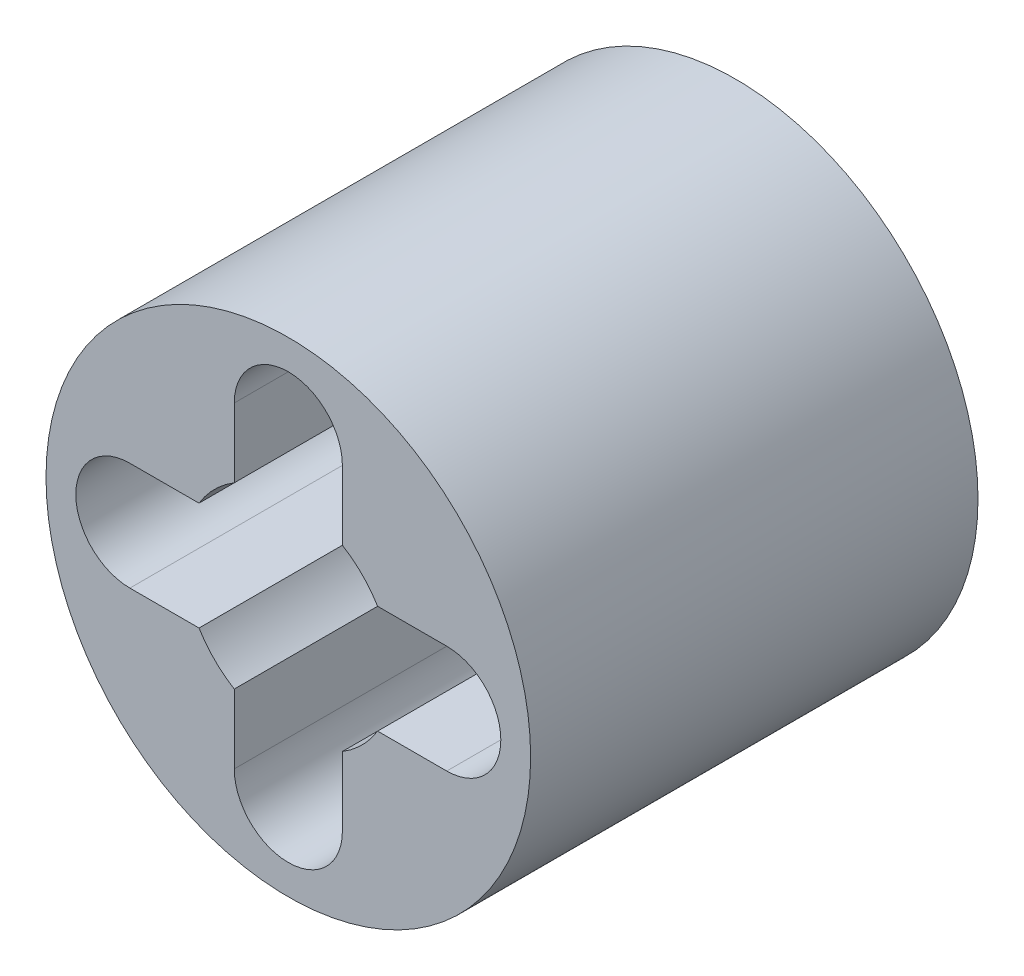
SolidWorks part; units mm, degrees
ref_plane "Plan de face" through (0, 0, 0) normal (0, 0, 1) x (1, 0, 0)
ref_plane "Plan de dessus" through (0, 0, 0) normal (0, 1, 0) x (1, 0, 0)
ref_plane "Plan de droite" through (0, 0, 0) normal (1, 0, 0) x (0, 0, -1)
sketch "Esquisse1" plane through (0, 0, 0) normal (0, 0, 1) x (1, 0, 0)
  line L0 (2.125, -0.725) -> (1.1977, -0.725)
  line L1 (2.125, 0.725) -> (1.1977, 0.725)
  line L2 (0.725, 2.125) -> (0.725, 1.1977)
  line L3 (-0.725, 2.125) -> (-0.725, 1.1977)
  line L4 (-2.125, 0.725) -> (-1.1977, 0.725)
  line L5 (-2.125, -0.725) -> (-1.1977, -0.725)
  line L6 (-0.725, -2.125) -> (-0.725, -1.1977)
  line L7 (0.725, -2.125) -> (0.725, -1.1977)
  circle A0 centre (0, 0) radius 3.25
  arc A1 (0.725, -1.1977) -> (1.1977, -0.725) centre (0, 0) ccw
  arc A2 (0.725, 2.125) -> (-0.725, 2.125) centre (0, 2.125) ccw
  arc A3 (2.125, -0.725) -> (2.125, 0.725) centre (2.125, 0) ccw
  arc A4 (-0.725, -2.125) -> (0.725, -2.125) centre (0, -2.125) ccw
  arc A5 (-2.125, 0.725) -> (-2.125, -0.725) centre (-2.125, 0) ccw
  arc A6 (-1.1977, -0.725) -> (-0.725, -1.1977) centre (0, 0) ccw
  arc A7 (-0.725, 1.1977) -> (-1.1977, 0.725) centre (0, 0) ccw
  arc A8 (1.1977, 0.725) -> (0.725, 1.1977) centre (0, 0) ccw
  point P14 (0, 0)
  dimension "D1" = 6.5
  dimension "D2" = 2.8
  dimension "D3" = 1.45
  dimension "D4" = 2.125
  dimension "D5" = 4
extrude "Boss.-Extru.1" add sketch "Esquisse1" along normal blind 6
